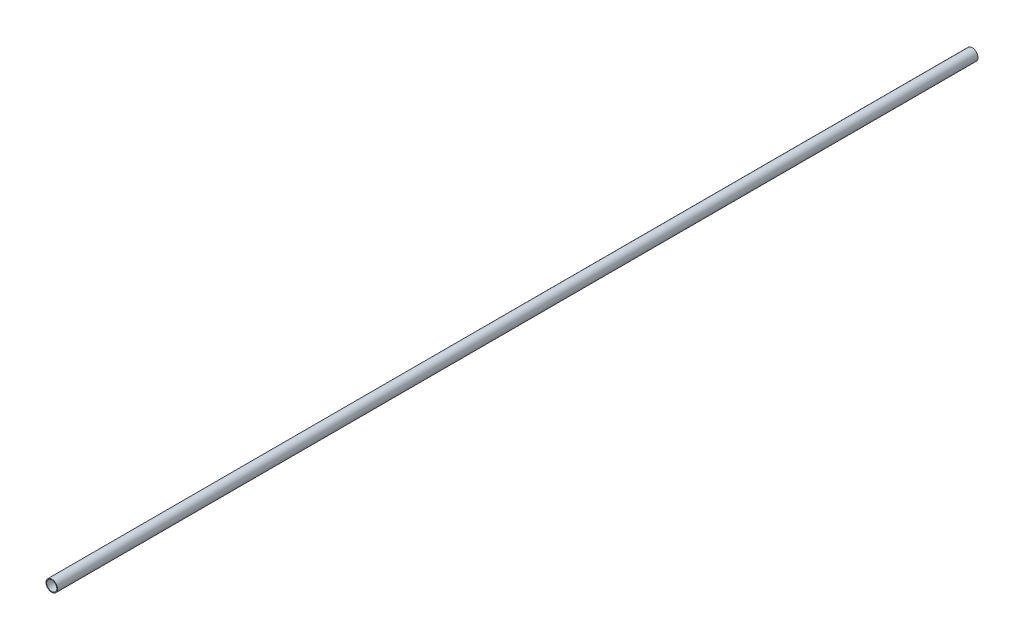
SolidWorks part; units mm, degrees
material "Carbon Fiber Tube - UD Approx"
ref_plane "Front Plane" through (0, 0, 0) normal (0, 0, 1) x (1, 0, 0)
ref_plane "Top Plane" through (0, 0, 0) normal (0, 1, 0) x (1, 0, 0)
ref_plane "Right Plane" through (0, 0, 0) normal (1, 0, 0) x (0, 0, -1)
sketch "Sketch1" plane through (0, 0, 0) normal (0, 0, 1) x (1, 0, 0)
  circle A0 centre (0, 0) radius 12.5
  circle A1 centre (0, 0) radius 11
  dimension "D1" = 25
  dimension "D2" = 22
extrude "Boss-Extrude1" add sketch "Sketch1" along normal blind 2000
